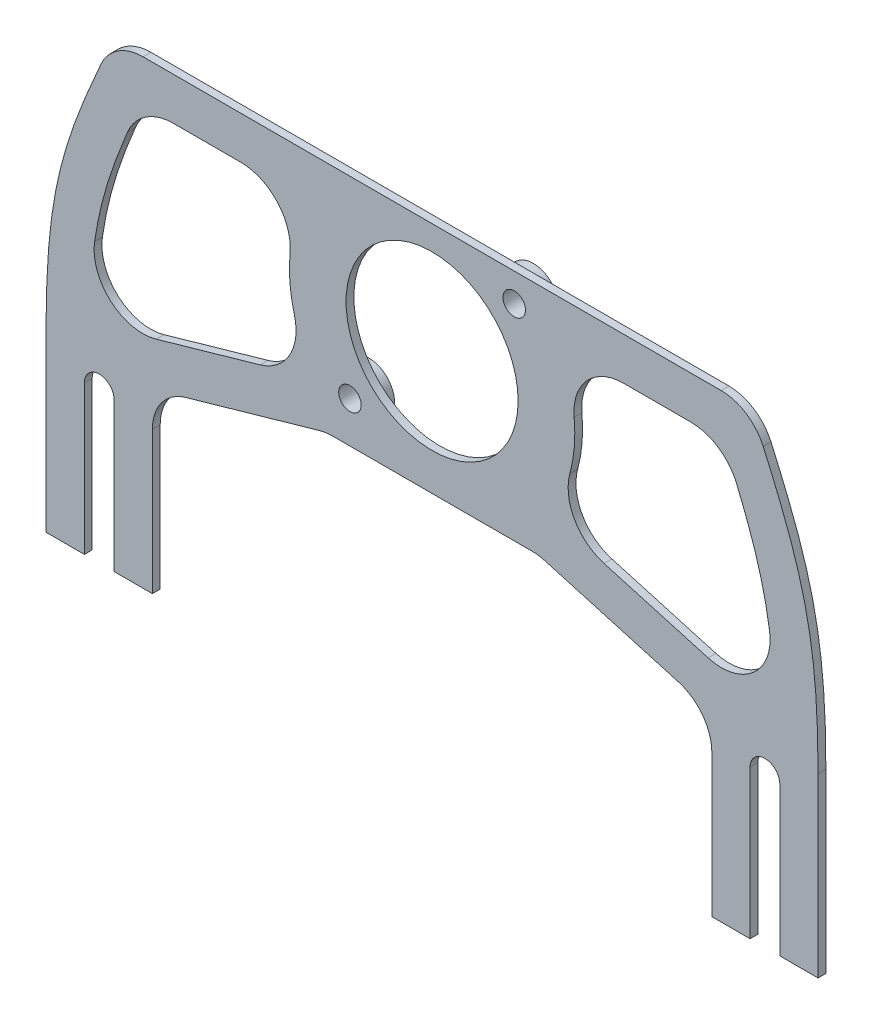
SolidWorks part; units mm, degrees
ref_plane "Front Plane" through (0, 0, 0) normal (0, 0, 1) x (1, 0, 0)
ref_plane "Top Plane" through (0, 0, 0) normal (0, 1, 0) x (1, 0, 0)
ref_plane "Right Plane" through (0, 0, 0) normal (1, 0, 0) x (0, 0, -1)
sketch "Sketch2" plane through (0, 0, 0) normal (0, 0, 1) x (1, 0, 0)
  line L0 (-14.7276, 48.0148) -> (0, 62.7424) construction
  line L1 (0, 0) -> (0, 107.3504) construction
  line L5 (0, 0) -> (-57.023, 0) construction
  line L7 (-59.69, 0) -> (-59.69, 12.7) construction
  line L10 (-69.215, 12.7) -> (-69.215, 0)
  line L11 (-69.215, 0) -> (-62.357, 0)
  line L12 (-50.165, 12.7) -> (-50.165, 0) construction
  line L16 (-50.165, 31.75) -> (50.165, 31.75) construction
  line L18 (-57.15, 82.55) -> (57.15, 82.55)
  line L19 (-50.165, 0) -> (-50.165, 31.75)
  line L20 (-69.215, 12.7) -> (-69.215, 31.75)
  line L26 (-59.69, 0) -> (-59.69, 26.67) construction
  line L29 (-62.357, 0) -> (-62.357, 26.67)
  line L30 (-57.023, 0) -> (-57.023, 26.67)
  line L31 (-57.023, 0) -> (-50.165, 0)
  line L32 (-62.357, 0) -> (-57.023, 0) construction
  line L33 (22.3351, 62.7424) -> (-22.3351, 62.7424) construction
  line L34 (0, 62.7424) -> (14.7276, 77.47) construction
  line L36 (62.357, 0) -> (57.023, 0) construction
  line L37 (59.69, 0) -> (59.69, 26.67) construction
  line L39 (50.165, 12.7) -> (50.165, 0) construction
  line L40 (59.69, 0) -> (59.69, 12.7) construction
  line L41 (57.023, 0) -> (50.165, 0)
  line L42 (57.023, 0) -> (57.023, 26.67)
  line L43 (62.357, 0) -> (62.357, 26.67)
  line L44 (69.215, 12.7) -> (69.215, 31.75)
  line L45 (50.165, 0) -> (50.165, 31.75)
  line L46 (69.215, 0) -> (62.357, 0)
  line L47 (69.215, 12.7) -> (69.215, 0)
  line L49 (-50.165, 31.75) -> (-19.05, 40.64)
  line L50 (-19.05, 40.64) -> (0, 40.64)
  line L51 (0, 40.64) -> (19.05, 40.64)
  line L52 (19.05, 40.64) -> (50.165, 31.75)
  circle A4 centre (0, 62.7424) radius 15.4305
  circle A5 centre (-14.7276, 48.0148) radius 2.0193
  arc A10 (-57.023, 26.67) -> (-62.357, 26.67) centre (-59.69, 26.67) ccw
  circle A11 centre (14.7276, 77.47) radius 2.0193
  arc A12 (57.023, 26.67) -> (62.357, 26.67) centre (59.69, 26.67) cw
  circle A13 centre (0, 62.7424) radius 19.05 construction
  spline S0 degree 3 poles (-69.215, 31.75) (-69.215, 54.2017) (-66.0802, 63.0773) (-57.15, 82.55) knots 0 0 0 0 1 1 1 1
  spline S1 degree 3 poles (69.215, 31.75) (69.215, 54.2017) (66.0802, 63.0773) (57.15, 82.55) knots 0 0 0 0 1 1 1 1
  point P0 (0, 31.75)
  point P16 (0, 44.45)
  point P39 (0, 82.55)
  point P42 (0, 82.55)
  point P48 (0, 78.1729)
  dimension "D3" = 50.165
  dimension "D4" = 38.1
  dimension "D9" = 5.08
  dimension "D11" = 4.0386
  dimension "D2" = 15.4305
  dimension "D5" = 19.05
  dimension "D6" = 5.08
  dimension "D7" = 5.334
  dimension "D8" = 20.828
  dimension "D10" = 31.75
  dimension "D12" = 57.15
  dimension "D13" = 50.8
  dimension "D14" = 45
  dimension "D15" = 8.89
  dimension "D16" = 19.05
extrude "Boss-Extrude1" add sketch "Sketch2" along normal blind 1.4
fillet "Fillet4" radius 8.255 6 edges at (57.15, 82.55, 0.7) (-57.15, 82.55, 0.7) (50.165, 31.75, 0.7) (19.05, 40.64, 0.7) (-19.05, 40.64, 0.7) (-50.165, 31.75, 0.7)
sketch "Sketch7" plane through (0, 0, 1.4) normal (0, 0, 1) x (1, 0, 0)
  line L0 (-22.5019, 74.93) -> (-51.8273, 74.93)
  line L1 (-52.4073, 74.5535) -> (-52.2395, 74.93)
  line L2 (51.8273, 74.93) -> (-51.8273, 74.93)
  line L3 (-52.2395, 74.93) -> (-51.8273, 74.93)
  line L4 (-49.5023, 39.8643) -> (-46.2712, 40.7874)
  line L7 (-46.2712, 40.7874) -> (-22.255, 47.6492)
  line L8 (-46.2712, 40.7874) -> (-20.9358, 48.0261)
  arc A2 (-51.8273, 74.93) -> (-52.4073, 74.5535) centre (-51.8273, 74.295) ccw
  circle A4 centre (0, 62.7424) radius 25.5905
  arc A5 (-22.5019, 74.93) -> (-20.9358, 48.0261) centre (0, 62.7424) ccw
  arc A6 (-60.5215, 49.5371) -> (-49.5023, 39.8643) centre (-51.8977, 48.2484) ccw
  arc A7 (-46.2712, 40.7874) -> (-57.785, 25.5232) centre (-41.91, 25.5232) ccw
  spline S2 degree 3 poles (481.5028, 2000.865) (88.7971, 308.93) (-29.2367, 130.7486) (-55.5586, 67.182) (-56.2136, 65.5133) (-57.3868, 62.2938) (-57.9052, 60.7431) (-58.8234, 57.6762) (-59.2236, 56.1598) (-59.9228, 53.0675) (-60.222, 51.4911) (-60.7301, 48.1838) (-60.9388, 46.4525) (-66.7416, -18.3555) (-22.4523, -221.5015) (3.3413, -1966.9675) knots -4.255246 -4.255246 -4.255246 -4.255246 0.125 0.125 0.25 0.25 0.375 0.375 0.5 0.5 0.625 0.625 0.75 0.75 4.999932 4.999932 4.999932 4.999932 only from (-52.4073, 74.5535) to (-61.595, 31.75)
  spline S3 degree 3 poles (-52.4073, 74.5535) (-53.2924, 72.5678) (-54.098, 70.7094) (-55.5586, 67.182) (-56.2136, 65.5133) (-57.3868, 62.2938) (-57.9052, 60.7431) (-58.8234, 57.6762) (-59.2236, 56.1598) (-59.9228, 53.0675) (-60.222, 51.4911) (-60.4914, 49.7376) (-60.5065, 49.6375) (-60.5215, 49.5371) knots 0 0 0 0 0.125 0.125 0.25 0.25 0.375 0.375 0.5 0.5 0.625 0.625 0.632546 0.632546 0.632546 0.632546
  point P3 (-60.5233, 49.5257)
  point P6 (-60.5233, 49.5257)
  point P9 (-51.8273, 48.2484)
  dimension "D4" = 8.7196
  dimension "D1" = 7.62
  dimension "D2" = 7.62
  dimension "D3" = 10.16
extrude "Cut-Extrude1" cut sketch "Sketch7" against normal through all
fillet "Fillet5" radius 8.89 3 edges at (-22.5019, 74.93, 0.7) (-52.2395, 74.93, 0.7) (-20.9358, 48.0261, 0.7)
mirror "Mirror1" about plane through (0, 0, 0) normal (1, 0, 0) of "Fillet5", "Cut-Extrude1"
sketch "Sketch8" plane through (0, 0, 0) normal (0, 0, -1) x (-1, 0, 0)
  circle A0 centre (-14.7276, 77.47) radius 4.5593
  circle A2 centre (-14.7276, 77.47) radius 2.0193 construction
  circle A3 centre (-14.7276, 77.47) radius 2.0193
  circle A4 centre (14.7276, 48.0148) radius 4.5593
  circle A5 centre (14.7276, 48.0148) radius 2.0193 construction
  circle A6 centre (14.7276, 48.0148) radius 2.0193
  dimension "D1" = 2.54
extrude "Boss-Extrude2" add sketch "Sketch8" along normal offset from surface (2.029 mm away) 3.429 up to face at (-41.1336, 60.9893, 1.4)
